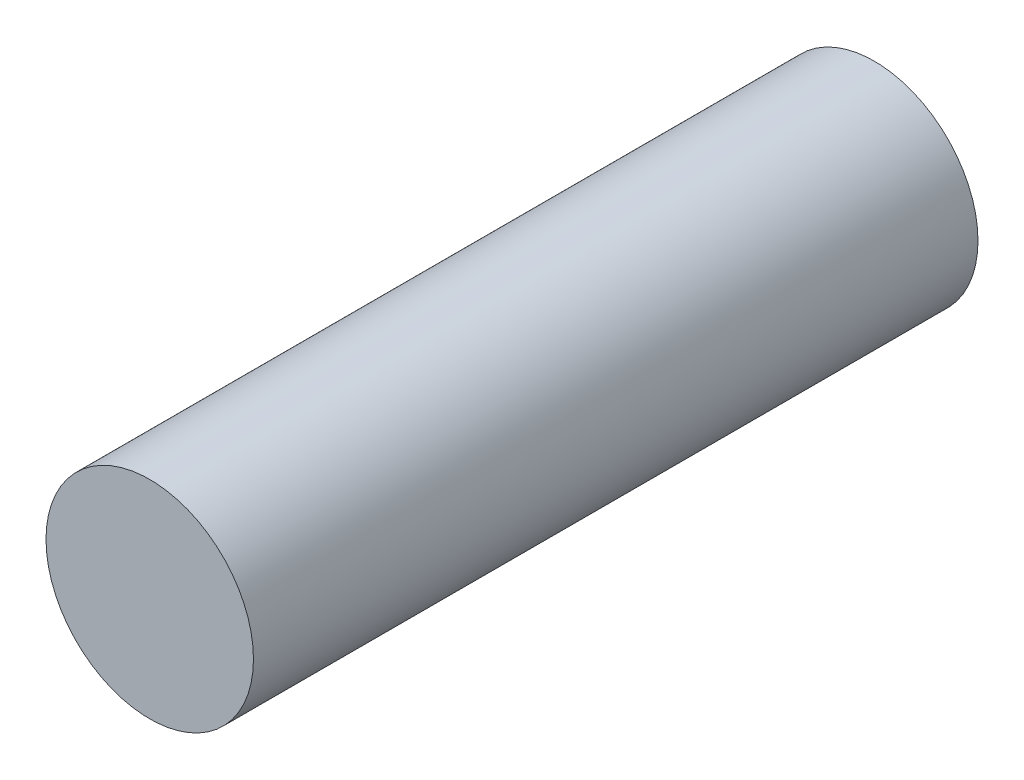
SolidWorks part; units mm, degrees
ref_plane "Front Plane" through (0, 0, 0) normal (0, 0, 1) x (1, 0, 0)
ref_plane "Top Plane" through (0, 0, 0) normal (0, 1, 0) x (1, 0, 0)
ref_plane "Right Plane" through (0, 0, 0) normal (1, 0, 0) x (0, 0, -1)
sketch "Sketch1" plane through (0, 0, 0) normal (0, 0, 1) x (1, 0, 0)
  circle A0 centre (0, 0) radius 16.75
  dimension "D1" = 33.5
extrude "Boss-Extrude1" add sketch "Sketch1" along normal blind 117
